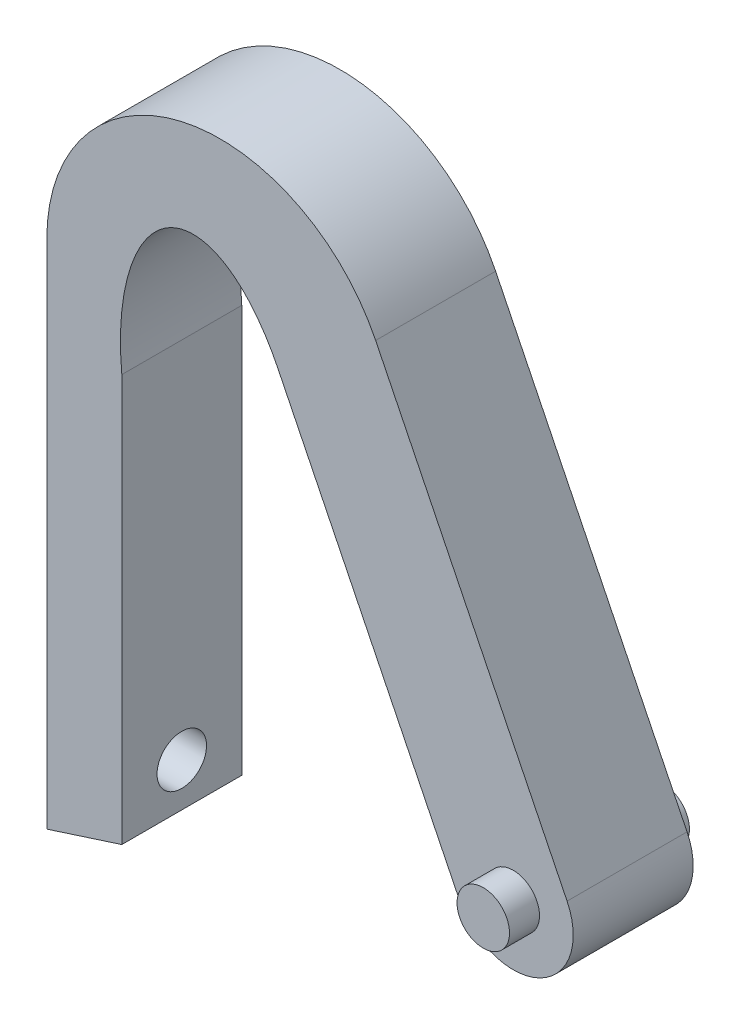
SolidWorks part; units mm, degrees
ref_plane "Alzado" through (0, 0, 0) normal (0, 0, 1) x (1, 0, 0)
ref_plane "Planta" through (0, 0, 0) normal (0, 1, 0) x (1, 0, 0)
ref_plane "Vista lateral" through (0, 0, 0) normal (1, 0, 0) x (0, 0, -1)
sketch "Croquis1" plane through (0, 0, 0) normal (0, 0, 1) x (1, 0, 0)
  line L0 (-21.6261, 28.2862) -> (-8.8598, 2.2894)
  line L1 (-28.1624, 23.4473) -> (-16.0407, -1.2369)
  line L2 (-43.554, 23.1926) -> (-43.554, -10.8995)
  line L3 (-38.554, 17.8499) -> (-38.554, -9.2921)
  line L4 (-38.554, -9.2921) -> (-43.554, -10.8995)
  arc A0 (-16.0407, -1.2369) -> (-8.8598, 2.2894) centre (-12.4503, 0.5262) ccw
  arc A1 (-21.6261, 28.2862) -> (-43.554, 23.1926) centre (-31.9985, 23.1926) ccw
  ellipse E0 centre (-32.4427, 17.334) end of major axis (-30.5249, 6.3818) minor radius 5.9901 (-28.1624, 23.4473) -> (-38.554, 17.8499) ccw
  dimension "D1" = 8
  dimension "D3" = 5
  dimension "D2" = 27.5
extrude "Saliente-Extruir1" add sketch "Croquis1" along normal blind 8
sketch "Croquis2" plane through (0, 0, 8) normal (0, 0, 1) x (1, 0, 0)
  circle A0 centre (-12.4503, 0.5262) radius 1.75
  dimension "D1" = 3.5
extrude "Saliente-Extruir2" add sketch "Croquis2" along normal blind 2
ref_plane "Plano1" through (0, 0, 4) normal (0, 0, 1) x (1, 0, 0)
mirror "Simetría1" about plane through (0, 0, 4) normal (0, 0, 1) of "Saliente-Extruir2"
hole_wizard "Perforador para roscar para macho de roscar para M41" positions "Croquis4" profile "Croquis3" hole size "M4" standard "ISO"
sketch "Croquis4" plane through (-43.554, 0, 0) normal (-1, 0, 0) x (0, 0, 1)
  line L0 (4, -10.8995) -> (4, 3.2002) construction
  line L1 (8, -10.8995) -> (0, -10.8995) construction
  point P0 (4, -6.3995)
  dimension "D1" = 4.5
sketch "Croquis3" plane through (-43.554, -6.3995, 4) normal (0, 1, 0) x (0, 0, 1)
  line L0 (0, 0) -> (0, 7.9914)
  line L1 (0, 7.9914) -> (1.65, 7)
  line L2 (1.65, 7) -> (1.65, 0)
  line L5 (1.65, 0) -> (0, 0)
  line L10 (0, 7.9914) -> (-1.65, 7) construction
  line L11 (0, -6.35) -> (0, 107.95) construction
  dimension "Diámetro de taladro" = 3.3
  dimension "Profundidad de taladro" = 7
  dimension "Ángulo de perforador" = 118
